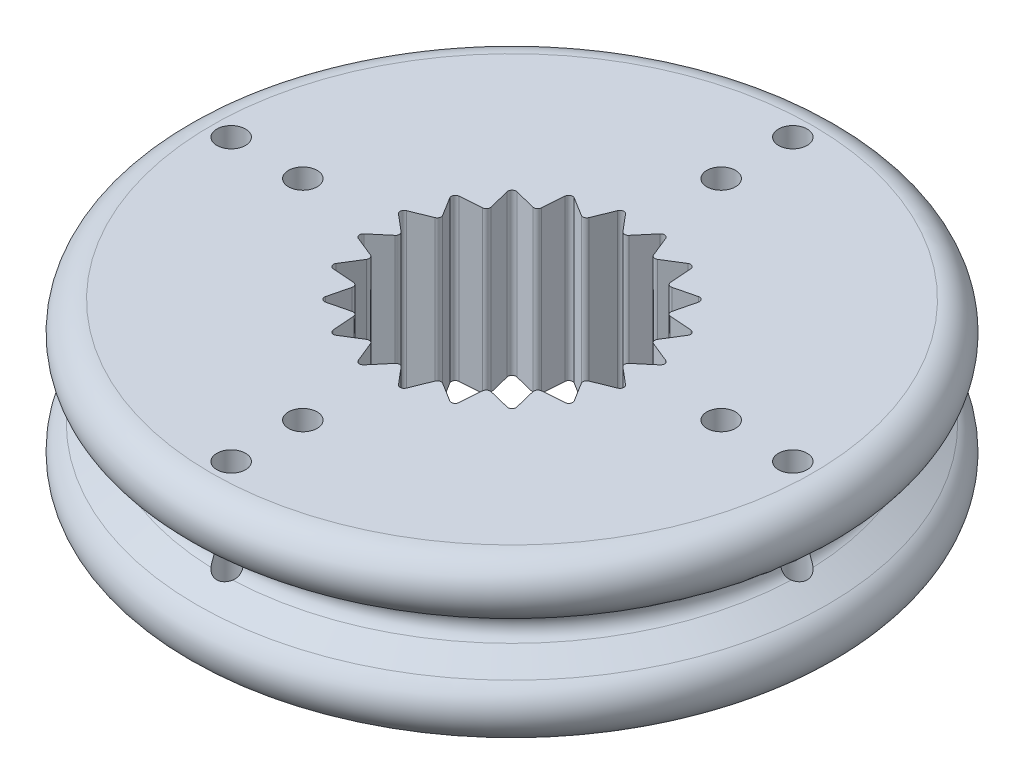
SolidWorks part; units mm, degrees
ref_plane "Front Plane" through (0, 0, 0) normal (0, 0, 1) x (1, 0, 0)
ref_plane "Top Plane" through (0, 0, 0) normal (0, 1, 0) x (1, 0, 0)
ref_plane "Right Plane" through (0, 0, 0) normal (1, 0, 0) x (0, 0, -1)
sketch "Sketch1" plane through (0, 0, 0) normal (1, 0, 0) x (0, 0, -1)
  line L0 (0, 0) -> (0, 2.8) construction
  line L1 (-2.4, 2.8) -> (-5.25, 2.8)
  line L2 (-5.5, 1.867) -> (-5.0662, 1.6165)
  line L3 (-5.0662, 1.1835) -> (-5.5, 0.933)
  line L4 (-5.25, 0) -> (-2.4, 0)
  line L5 (-2.4, 2.8) -> (-2.4, 0)
  arc A0 (-5.0662, 1.1835) -> (-5.0662, 1.6165) centre (-5.1912, 1.4) ccw
  arc A1 (-5.5, 0.933) -> (-5.25, 0) centre (-5.25, 0.5) ccw
  arc A2 (-5.25, 2.8) -> (-5.5, 1.867) centre (-5.25, 2.3) ccw
  point P6 (-4.9412, 1.4)
  point P13 (-7.116, 2.8)
  dimension "D3" = 0.25
  dimension "D4" = 0.5
  dimension "D1" = 2.8
  dimension "D2" = 2.4
  dimension "D5" = 9.8823
  dimension "D6" = 60
  dimension "D7" = 11.5
revolve "Revolve1" add sketch "Sketch1" angle 360 about L0
sketch "Sketch2" plane through (0, 0, 0) normal (1, 0, 0) x (0, 0, -1)
  circle A0 centre (0, 1.4) radius 0.25
  dimension "D1" = 0.5
  dimension "D2" = 1.4
extrude "Cut-Extrude1" cut sketch "Sketch2" against normal blind 10 from offset 3.65 offset against normal yes
sketch "Sketch3" plane through (0, 2.8, 0) normal (0, 1, 0) x (1, 0, 0)
  circle A0 centre (3.65, 0) radius 0.25
  circle A1 centre (4.9, 0) radius 0.25
  circle A3 centre (0, 0) radius 2.4 construction
  dimension "D1" = 0.5
  dimension "D3" = 1
  dimension "D2" = 1.25
extrude "Cut-Extrude2" cut sketch "Sketch3" against normal through all both and the other way through all
pattern_circular "CirPattern1" count 4 over 360 about axis through (0, 0, 0) along (0, 1, 0) of "Cut-Extrude2", "Cut-Extrude1"
sketch "Sketch4" plane through (0, 0, 0) normal (0, 1, 0) x (1, 0, 0)
  line L0 (0, 0) -> (0, 2.4) construction
  line L1 (0, 1.925) -> (-0.3754, 2.3705)
  line L2 (0, 1.925) -> (0.3754, 2.3705)
  line L3 (0.5949, 1.8308) -> (0.3754, 2.3705)
  line L4 (0.5949, 1.8308) -> (1.0896, 2.1384)
  line L5 (1.1315, 1.5574) -> (1.0896, 2.1384)
  line L6 (1.1315, 1.5574) -> (1.6971, 1.6971)
  line L7 (1.5574, 1.1315) -> (1.6971, 1.6971)
  line L8 (1.5574, 1.1315) -> (2.1384, 1.0896)
  line L9 (1.8308, 0.5949) -> (2.1384, 1.0896)
  line L10 (1.8308, 0.5949) -> (2.3705, 0.3754)
  line L11 (1.925, 0) -> (2.3705, 0.3754)
  line L12 (1.925, 0) -> (2.3705, -0.3754)
  line L13 (1.8308, -0.5949) -> (2.3705, -0.3754)
  line L14 (1.8308, -0.5949) -> (2.1384, -1.0896)
  line L15 (1.5574, -1.1315) -> (2.1384, -1.0896)
  line L16 (1.5574, -1.1315) -> (1.6971, -1.6971)
  line L17 (1.1315, -1.5574) -> (1.6971, -1.6971)
  line L18 (1.1315, -1.5574) -> (1.0896, -2.1384)
  line L19 (0.5949, -1.8308) -> (1.0896, -2.1384)
  line L20 (0.5949, -1.8308) -> (0.3754, -2.3705)
  line L21 (0, -1.925) -> (0.3754, -2.3705)
  line L22 (0, -1.925) -> (-0.3754, -2.3705)
  line L23 (-0.5949, -1.8308) -> (-0.3754, -2.3705)
  line L24 (-0.5949, -1.8308) -> (-1.0896, -2.1384)
  line L25 (-1.1315, -1.5574) -> (-1.0896, -2.1384)
  line L26 (-1.1315, -1.5574) -> (-1.6971, -1.6971)
  line L27 (-1.5574, -1.1315) -> (-1.6971, -1.6971)
  line L28 (-1.5574, -1.1315) -> (-2.1384, -1.0896)
  line L29 (-1.8308, -0.5949) -> (-2.1384, -1.0896)
  line L30 (-1.8308, -0.5949) -> (-2.3705, -0.3754)
  line L31 (-1.925, 0) -> (-2.3705, -0.3754)
  line L32 (-1.925, 0) -> (-2.3705, 0.3754)
  line L33 (-1.8308, 0.5949) -> (-2.3705, 0.3754)
  line L34 (-1.8308, 0.5949) -> (-2.1384, 1.0896)
  line L35 (-1.5574, 1.1315) -> (-2.1384, 1.0896)
  line L36 (-1.5574, 1.1315) -> (-1.6971, 1.6971)
  line L37 (-1.1315, 1.5574) -> (-1.6971, 1.6971)
  line L38 (-1.1315, 1.5574) -> (-1.0896, 2.1384)
  line L39 (-0.5949, 1.8308) -> (-1.0896, 2.1384)
  line L40 (-0.5949, 1.8308) -> (-0.3754, 2.3705)
  line L41 (0, 0) -> (0, 1.925) construction
  circle A0 centre (0, 0) radius 2.4 construction
  arc A1 (0.3754, 2.3705) -> (-0.3754, 2.3705) centre (0, 0) ccw
  circle A2 centre (0, 0) radius 1.925 construction
  arc A3 (-0.3754, 2.3705) -> (0.3754, 2.3705) centre (0, 0) ccw construction
  circle A4 centre (0, 0) radius 1.925 construction
  arc A5 (1.0896, 2.1384) -> (0.3754, 2.3705) centre (0, 0) ccw
  circle A6 centre (0, 0) radius 1.925 construction
  arc A7 (1.6971, 1.6971) -> (1.0896, 2.1384) centre (0, 0) ccw
  circle A8 centre (0, 0) radius 1.925 construction
  arc A9 (2.1384, 1.0896) -> (1.6971, 1.6971) centre (0, 0) ccw
  circle A10 centre (0, 0) radius 1.925 construction
  arc A11 (2.3705, 0.3754) -> (2.1384, 1.0896) centre (0, 0) ccw
  circle A12 centre (0, 0) radius 1.925 construction
  arc A13 (2.3705, -0.3754) -> (2.3705, 0.3754) centre (0, 0) ccw
  circle A14 centre (0, 0) radius 1.925 construction
  arc A15 (2.1384, -1.0896) -> (2.3705, -0.3754) centre (0, 0) ccw
  circle A16 centre (0, 0) radius 1.925 construction
  arc A17 (1.6971, -1.6971) -> (2.1384, -1.0896) centre (0, 0) ccw
  circle A18 centre (0, 0) radius 1.925 construction
  arc A19 (1.0896, -2.1384) -> (1.6971, -1.6971) centre (0, 0) ccw
  circle A20 centre (0, 0) radius 1.925 construction
  arc A21 (0.3754, -2.3705) -> (1.0896, -2.1384) centre (0, 0) ccw
  circle A22 centre (0, 0) radius 1.925 construction
  arc A23 (-0.3754, -2.3705) -> (0.3754, -2.3705) centre (0, 0) ccw
  circle A24 centre (0, 0) radius 1.925 construction
  arc A25 (-1.0896, -2.1384) -> (-0.3754, -2.3705) centre (0, 0) ccw
  circle A26 centre (0, 0) radius 1.925 construction
  arc A27 (-1.6971, -1.6971) -> (-1.0896, -2.1384) centre (0, 0) ccw
  circle A28 centre (0, 0) radius 1.925 construction
  arc A29 (-2.1384, -1.0896) -> (-1.6971, -1.6971) centre (0, 0) ccw
  circle A30 centre (0, 0) radius 1.925 construction
  arc A31 (-2.3705, -0.3754) -> (-2.1384, -1.0896) centre (0, 0) ccw
  circle A32 centre (0, 0) radius 1.925 construction
  arc A33 (-2.3705, 0.3754) -> (-2.3705, -0.3754) centre (0, 0) ccw
  circle A34 centre (0, 0) radius 1.925 construction
  arc A35 (-2.1384, 1.0896) -> (-2.3705, 0.3754) centre (0, 0) ccw
  circle A36 centre (0, 0) radius 1.925 construction
  arc A37 (-1.6971, 1.6971) -> (-2.1384, 1.0896) centre (0, 0) ccw
  circle A38 centre (0, 0) radius 1.925 construction
  arc A39 (-1.0896, 2.1384) -> (-1.6971, 1.6971) centre (0, 0) ccw
  circle A40 centre (0, 0) radius 1.925 construction
  arc A41 (-0.3754, 2.3705) -> (-1.0896, 2.1384) centre (0, 0) ccw
  dimension "D1" = 3.85
  dimension "D3" = 1.925
  dimension "D2" = 20
extrude "Boss-Extrude1" add sketch "Sketch4" along normal up to surface (2.8 mm away) contours L10 A11 L9 | L12 A13 L11 | L14 A15 L13 | L16 A17 L15 | L20 A21 L19 | L22 A23 L21 | L8 A9 L7 | L6 A7 L5 | L4 A5 L3 | L2 A1 L1 | L40 A41 L39 | L38 A39 L37 | L36 A37 L35 | L34 A35 L33 | L32 A33 L31 | L30 A31 L29 | L28 A29 L27 | L26 A27 L25 | L24 A25 L23 | L18 A19 L17 up to face at (0, 2.8, -5.15)
fillet "Fillet1" radius 0.07 40 edges at (1.925, 1.4, 0) (2.3705, 1.4, -0.3754) (1.8308, 1.4, -0.5949) (2.1384, 1.4, -1.0896) (1.5574, 1.4, -1.1315) (1.6971, 1.4, -1.6971) (1.1315, 1.4, -1.5574) (1.0896, 1.4, -2.1384) (0.5949, 1.4, -1.8308) (0.3754, 1.4, -2.3705) (0, 1.4, -1.925) (-0.3754, 1.4, -2.3705) (-0.5949, 1.4, -1.8308) (-1.0896, 1.4, -2.1384) (-1.1315, 1.4, -1.5574) (-1.6971, 1.4, -1.6971) (-2.1384, 1.4, -1.0896) (-1.8308, 1.4, -0.5949) (-2.3705, 1.4, -0.3754) (-1.925, 1.4, 0) (-2.3705, 1.4, 0.3754) (-1.8308, 1.4, 0.5949) (-2.1384, 1.4, 1.0896) (-1.5574, 1.4, 1.1315) (-1.6971, 1.4, 1.6971) (-1.1315, 1.4, 1.5574) (-1.0896, 1.4, 2.1384) (-0.5949, 1.4, 1.8308) (-0.3754, 1.4, 2.3705) (0, 1.4, 1.925) (0.3754, 1.4, 2.3705) (0.5949, 1.4, 1.8308) (1.0896, 1.4, 2.1384) (1.1315, 1.4, 1.5574) (1.6971, 1.4, 1.6971) (1.5574, 1.4, 1.1315) (2.1384, 1.4, 1.0896) (1.8308, 1.4, 0.5949) (2.3705, 1.4, 0.3754) (-1.5574, 1.4, -1.1315)
equation "\"D2@Sketch2\"=\"D1@Sketch1\"/2"
